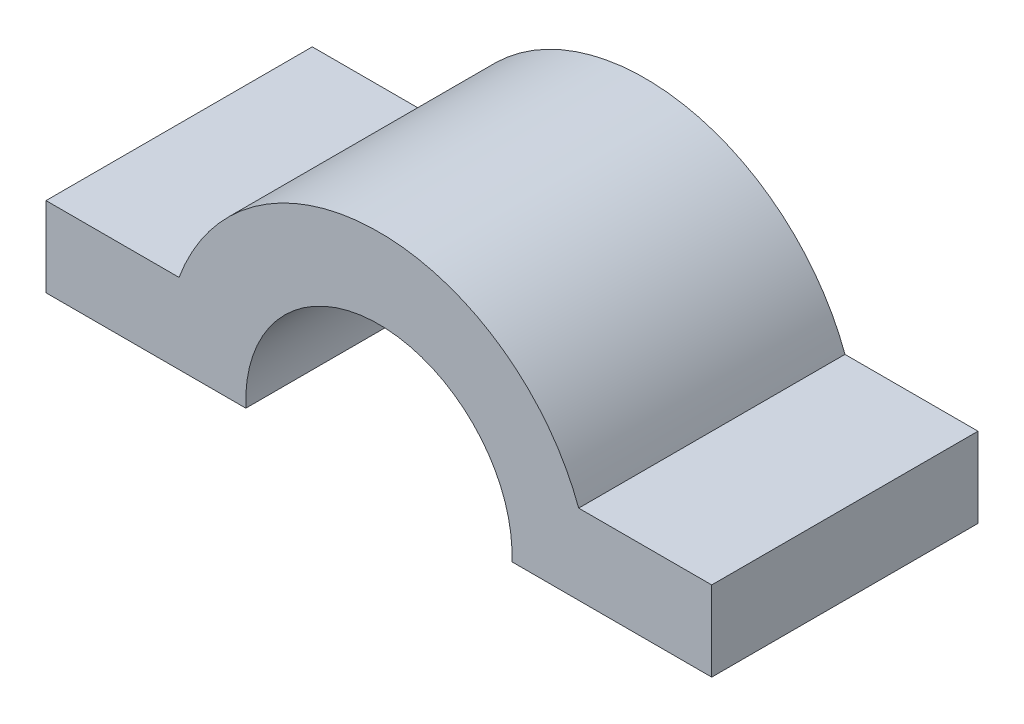
SolidWorks part; units mm, degrees
ref_plane "Front Plane" through (0, 0, 0) normal (0, 0, 1) x (1, 0, 0)
ref_plane "Top Plane" through (0, 0, 0) normal (0, 1, 0) x (1, 0, 0)
ref_plane "Right Plane" through (0, 0, 0) normal (1, 0, 0) x (0, 0, -1)
sketch "Sketch1" plane through (0, 0, 0) normal (0, 0, 1) x (1, 0, 0)
  line L0 (0, 0) -> (190.6323, 0)
  line L1 (190.6323, 0) -> (190.6323, 76.2)
  line L2 (190.6323, 76.2) -> (63.7455, 76.2)
  line L3 (-253.7354, 0) -> (-444.3677, 0)
  line L4 (-444.3677, 0) -> (-444.3677, 76.2)
  line L5 (-444.3677, 76.2) -> (-317.4809, 76.2)
  arc A0 (0, 0) -> (-253.7354, 0) centre (-126.8677, 5.7952) ccw
  arc A1 (63.7455, 76.2) -> (-317.4809, 76.2) centre (-126.8677, 5.7952) ccw
  dimension "D1" = 203.2
  dimension "D2" = 127
  dimension "D4" = 76.2
  dimension "D3" = 635
extrude "Boss-Extrude1" add sketch "Sketch1" against normal blind 254
